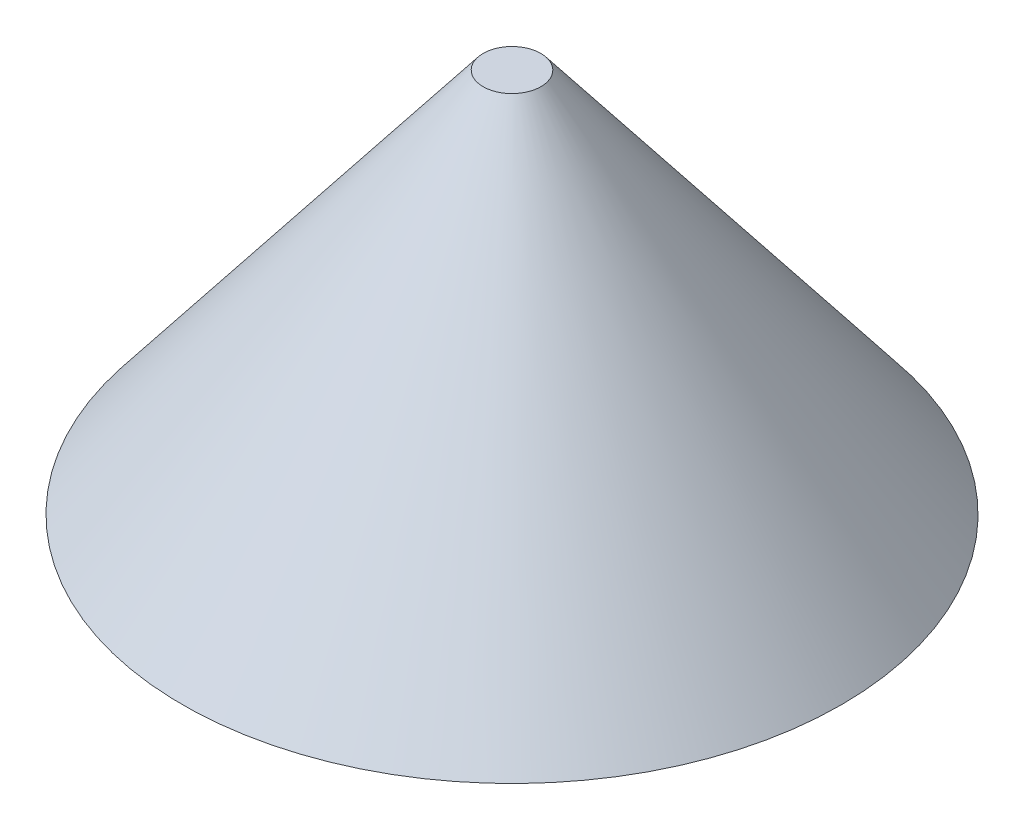
SolidWorks part; units mm, degrees
ref_plane "前视基准面" through (0, 0, 0) normal (0, 0, 1) x (1, 0, 0)
ref_plane "上视基准面" through (0, 0, 0) normal (0, 1, 0) x (1, 0, 0)
ref_plane "右视基准面" through (0, 0, 0) normal (1, 0, 0) x (0, 0, -1)
sketch "草图1" plane through (0, 0, 0) normal (0, 0, 1) x (1, 0, 0)
  line L0 (0, 0) -> (0, -60)
  line L1 (0, -60) -> (-51.3771, -60)
  line L2 (-51.3771, -60) -> (-4.5, 0)
  line L3 (-4.5, 0) -> (0, 0)
  dimension "D1" = 4.5
  dimension "D2" = 38
  dimension "D3" = 60
revolve "旋转1" add sketch "草图1" angle 360 about L0
